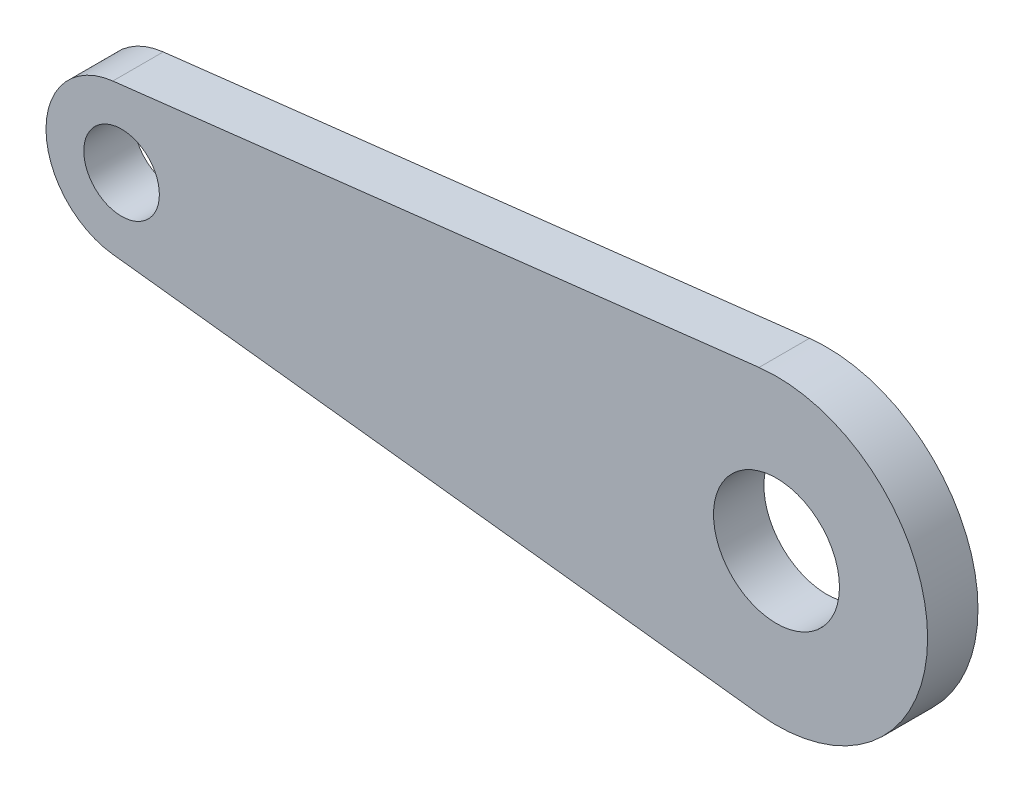
SolidWorks part; units mm, degrees
ref_plane "Přední rovina" through (0, 0, 0) normal (0, 0, 1) x (1, 0, 0)
ref_plane "Vrchní rovina" through (0, 0, 0) normal (0, 1, 0) x (1, 0, 0)
ref_plane "Pravá rovina" through (0, 0, 0) normal (1, 0, 0) x (0, 0, -1)
sketch "Skica2" plane through (0, 0, 0) normal (0, 0, 1) x (1, 0, 0)
  line L0 (-52.4315, 0) -> (312.4315, 0) construction
  line L1 (0, 60.1075) -> (0, -62.0031) construction
  line L2 (130, 63.075) -> (130, -67.6412) construction
  line L3 (-1.7308, 14.8998) -> (126.5385, 29.7996)
  line L4 (-1.7308, -14.8998) -> (126.5385, -29.7996)
  circle A0 centre (0, 0) radius 7.5
  arc A1 (-1.7308, 14.8998) -> (-1.7308, -14.8998) centre (0, 0) ccw
  circle A2 centre (130, 0) radius 12.5
  arc A3 (126.5385, -29.7996) -> (126.5385, 29.7996) centre (130, 0) ccw
  dimension "D2" = 15
  dimension "D3" = 30
  dimension "D4" = 60
  dimension "D5" = 25
  dimension "D1" = 130
extrude "Přidat vysunutím1" add sketch "Skica2" along normal blind 10
